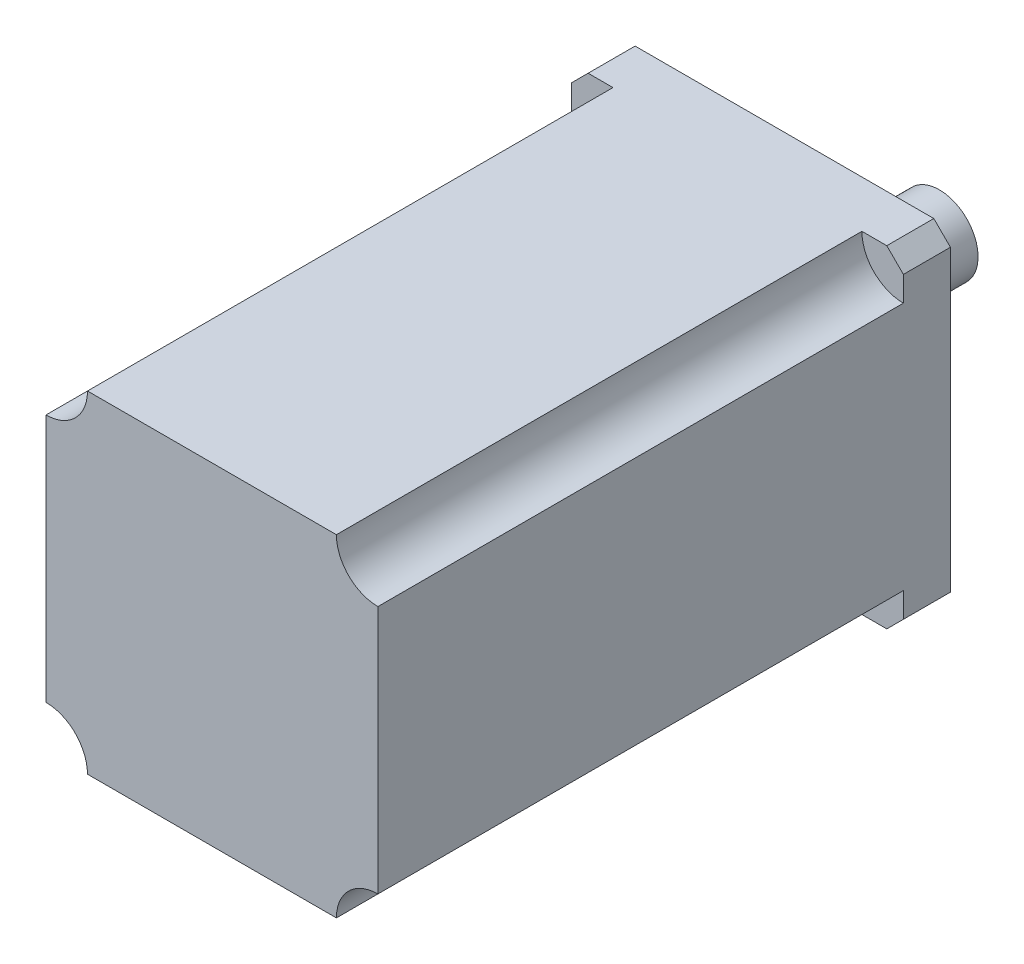
SolidWorks part; units mm, degrees
ref_plane "前视基准面" through (0, 0, 0) normal (0, 0, 1) x (1, 0, 0)
ref_plane "上视基准面" through (0, 0, 0) normal (0, 1, 0) x (1, 0, 0)
ref_plane "右视基准面" through (0, 0, 0) normal (1, 0, 0) x (0, 0, -1)
other "Configuration Table"
sketch "草图1" plane through (0, 0, 0) normal (0, 0, 1) x (1, 0, 0)
  line L0 (0, -30) -> (60, -30) construction
  line L1 (7.5, 0) -> (52.5, 0)
  line L2 (0, -7.5) -> (0, -52.5)
  line L3 (7.5, -60) -> (52.5, -60)
  line L4 (60, -7.5) -> (60, -52.5)
  line L5 (30, -60) -> (30, 0) construction
  arc A0 (52.5, 0) -> (60, -7.5) centre (60, 0) ccw
  arc A1 (52.5, -60) -> (60, -52.5) centre (60, -60) cw
  arc A2 (7.5, -60) -> (0, -52.5) centre (0, -60) ccw
  arc A3 (7.5, 0) -> (0, -7.5) centre (0, 0) cw
  dimension "D3" = 15
  dimension "D1" = 60
  dimension "D2" = 60
extrude "凸台-拉伸1" add sketch "草图1" along normal blind 95
sketch "草图3" plane through (0, 0, 0) normal (0, 0, -1) x (-1, 0, 0)
  line L1 (0, 0) -> (-60, 0)
  line L2 (0, 0) -> (0, -60)
  line L3 (0, -60) -> (-60, -60)
  line L4 (-60, 0) -> (-60, -60)
extrude "凸台-拉伸3" add sketch "草图3" along normal blind 8.5
sketch "草图5" plane through (0, 0, -8.5) normal (0, 0, -1) x (-1, 0, 0)
  line L0 (-60, -30) -> (0, -30) construction
  line L1 (-60, 0) -> (-60, -60) construction
  line L2 (-30, 0) -> (-30, -60) construction
  line L3 (0, -60) -> (0, 0) construction
  line L4 (0, 0) -> (-60, 0) construction
  line L5 (-60, -60) -> (0, -60) construction
  circle A0 centre (-30, -30) radius 25
  dimension "D1" = 50
extrude "凸台-拉伸5" add sketch "草图5" along normal blind 3
sketch "草图7" plane through (0, 0, -11.5) normal (0, 0, -1) x (-1, 0, 0)
  circle A0 centre (-30, -30) radius 7
  circle A1 centre (-30, -30) radius 25
  circle A2 centre (-30, -30) radius 25 construction
  dimension "D2" = 14
  dimension "D1" = 0
extrude "凸台-拉伸6" add sketch "草图7" along normal blind 25
chamfer "倒角1" distance 3 angle 45 4 edges at (60, -60, -4.25) (0, -60, -4.25) (0, 0, -4.25) (60, 0, -4.25)
